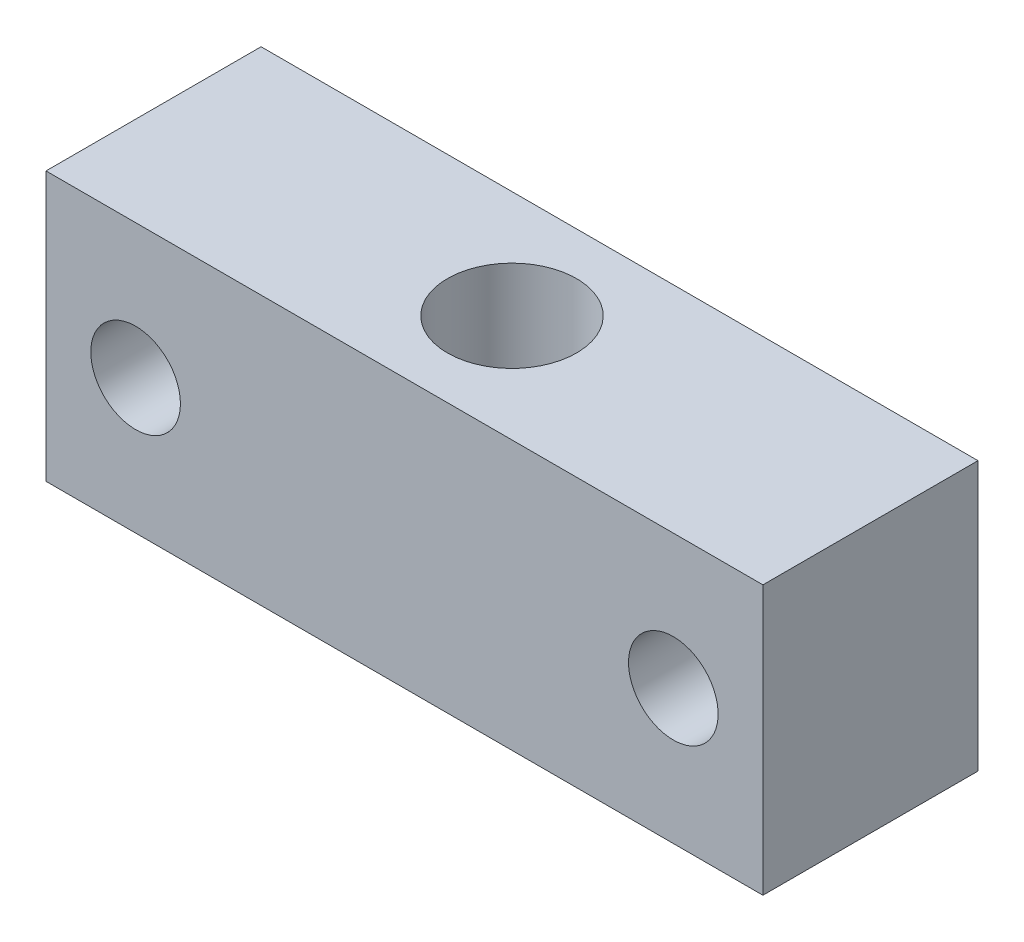
SolidWorks part; units mm, degrees
ref_plane "Спереди" through (0, 0, 0) normal (0, 0, 1) x (1, 0, 0)
ref_plane "Сверху" through (0, 0, 0) normal (0, 1, 0) x (1, 0, 0)
ref_plane "Справа" through (0, 0, 0) normal (1, 0, 0) x (0, 0, -1)
sketch "Эскиз1" plane through (0, 0, 0) normal (0, 1, 0) x (1, 0, 0)
  line L1 (-20, -6) -> (20, -6)
  line L2 (-20, -6) -> (-20, 6)
  line L3 (-20, 6) -> (20, 6)
  line L4 (20, -6) -> (20, 6)
  line L5 (-20, -6) -> (20, 6) construction
  line L6 (-20, 6) -> (20, -6) construction
  circle A0 centre (0, 0) radius 3.6
  point P0 (0, 0)
extrude "Бобышка-Вытянуть1" add sketch "Эскиз1" along normal blind 15
sketch "Эскиз2" plane through (0, 0, 6) normal (0, 0, 1) x (1, 0, 0)
  line L0 (0, 16.5544) -> (0, -1.7525) construction
  circle A0 centre (-15, 7.5) radius 2.5
  circle A1 centre (15, 7.5) radius 2.5
extrude "Вырез-Вытянуть1" cut sketch "Эскиз2" against normal through all
